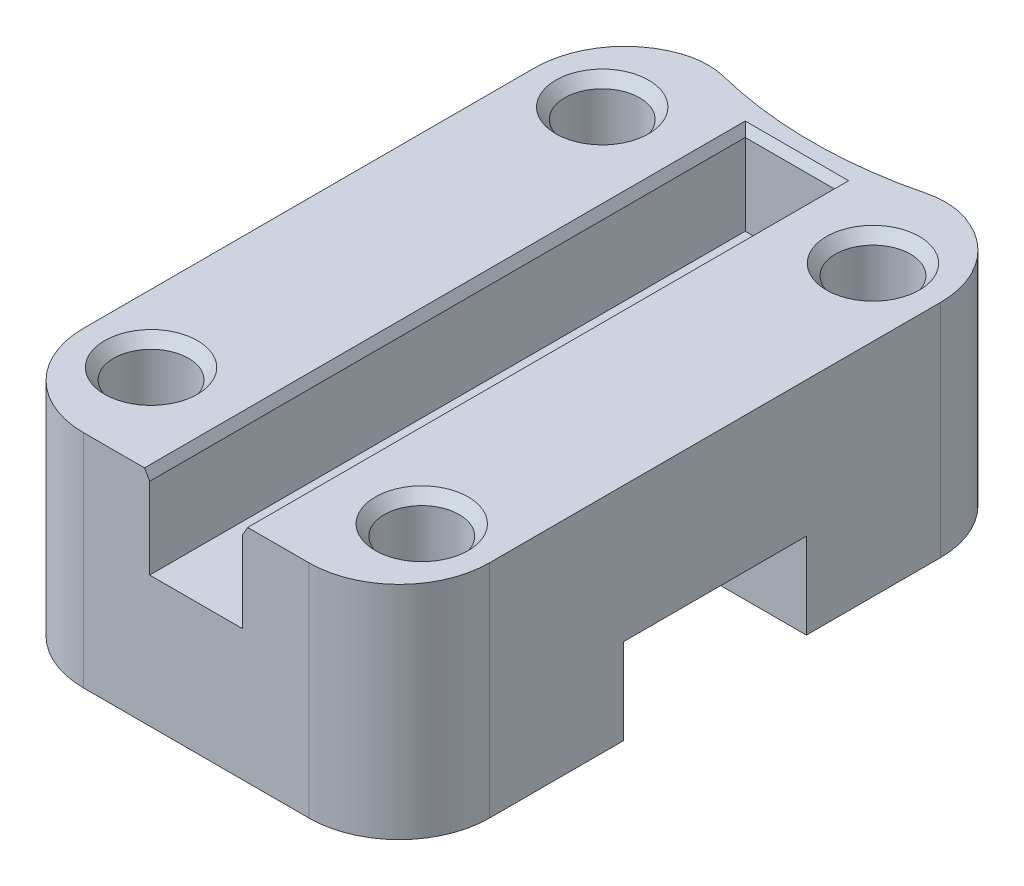
SolidWorks part; units mm, degrees
ref_plane "Спереди" through (0, 0, 0) normal (0, 0, 1) x (1, 0, 0)
ref_plane "Сверху" through (0, 0, 0) normal (0, 1, 0) x (1, 0, 0)
ref_plane "Справа" through (0, 0, 0) normal (1, 0, 0) x (0, 0, -1)
sketch "Sketch1" plane through (0, 0, 0) normal (0, 1, 0) x (1, 0, 0)
  line L1 (22.5, -35) -> (-22.5, -35)
  line L2 (22.5, -35) -> (22.5, 35)
  line L3 (22.5, 35) -> (-22.5, 35)
  line L4 (-22.5, -35) -> (-22.5, 35)
  line L5 (22.5, -35) -> (-22.5, 35) construction
  line L6 (22.5, 35) -> (-22.5, -35) construction
  point P0 (0, 0)
  dimension "D1" = 45
  dimension "D2" = 70
extrude "Boss-Extrude1" add sketch "Sketch1" along normal blind 14.5
sketch "Sketch2" plane through (22.5, 0, 0) normal (1, 0, 0) x (0, 0, -1)
  line L0 (0, 0) -> (0, 14.5) construction
  line L1 (-35, 0) -> (35, 0) construction
  line L2 (-35, 14.5) -> (35, 14.5) construction
  line L4 (10.125, 9.5) -> (-10.125, 9.5)
  line L5 (10.125, 9.5) -> (10.125, 0)
  line L6 (10.125, 0) -> (-10.125, 0)
  line L7 (-10.125, 9.5) -> (-10.125, 0)
  line L8 (10.125, 9.5) -> (-10.125, 0) construction
  line L9 (10.125, 0) -> (-10.125, 9.5) construction
  point P6 (0, 4.75)
  dimension "D1" = 20.25
  dimension "D2" = 9.5
extrude "Cut-Extrude1" cut sketch "Sketch2" against normal through all and the other way through all
sketch "Sketch3" plane through (0, 0, 0) normal (0, -1, 0) x (1, 0, 0)
  line L0 (15, -25) -> (15, 25) construction
  line L1 (-15, 25) -> (-15, -25) construction
  line L2 (-15, -25) -> (15, 25) construction
  line L3 (-22.5, -25) -> (22.5, -25) construction
  line L4 (-22.5, -35) -> (-22.5, -10.125) construction
  line L5 (22.5, -10.125) -> (22.5, -35) construction
  line L6 (-22.5, 25) -> (22.5, 25) construction
  line L7 (-22.5, 10.125) -> (-22.5, 35) construction
  line L8 (22.5, 35) -> (22.5, 10.125) construction
  line L9 (-15, 25) -> (15, -25) construction
  circle A0 centre (15, 25) radius 4.15
  circle A1 centre (15, -25) radius 4.15
  circle A2 centre (-15, -25) radius 4.15
  circle A3 centre (-15, 25) radius 4.15
  point P4 (0, 0)
  dimension "D1" = 8.3
  dimension "D2" = 30
  dimension "D3" = 50
extrude "Cut-Extrude2" cut sketch "Sketch3" against normal through all
sketch "Sketch5" plane through (0, 14.5, 0) normal (0, 1, 0) x (1, 0, 0)
  line L0 (5.15, 35) -> (-5.15, -35) construction
  line L1 (-5.15, -35) -> (-22.5, -35)
  line L2 (-5.15, -35) -> (-5.15, 35) construction
  line L3 (-5.15, 35) -> (-22.5, 35) construction
  line L4 (-22.5, -35) -> (-22.5, 35)
  line L5 (-5.15, -35) -> (-22.5, 35) construction
  line L6 (-5.15, 35) -> (-22.5, -35) construction
  line L7 (5.15, -35) -> (22.5, -35)
  line L8 (5.15, -35) -> (5.15, 35) construction
  line L9 (5.15, 35) -> (22.5, 35) construction
  line L10 (22.5, -35) -> (22.5, 35)
  line L11 (5.15, -35) -> (22.5, 35) construction
  line L12 (5.15, 35) -> (22.5, -35) construction
  line L13 (5.15, -35) -> (-5.15, 35) construction
  line L14 (-5.15, -35) -> (-5.15, 31)
  line L15 (-5.15, 31) -> (5.15, 31)
  line L16 (5.15, 31) -> (5.1302, -34.9493)
  line L17 (5.15, -35) -> (5.1302, -34.9493)
  line L18 (-22.5, 35) -> (22.5, 35)
  circle A0 centre (-15, 25) radius 4.15
  circle A1 centre (15, 25) radius 4.15
  circle A2 centre (15, -25) radius 4.15
  circle A3 centre (-15, -25) radius 4.15
  point P0 (-13.825, 0)
  point P6 (13.825, 0)
  point P12 (0, 0)
  dimension "D1" = 10.3
  dimension "D2" = 4
extrude "Boss-Extrude2" add sketch "Sketch5" along normal blind 10
chamfer "Chamfer1" distance 1 angle 50 4 edges at (15, 24.5, 29.15) (-15, 24.5, 29.15) (-15, 24.5, -20.85) (15, 24.5, -20.85)
chamfer "Chamfer2" distance 1 angle 30 3 edges at (-5.15, 24.5, 2) (0, 24.5, -31) (5.1401, 24.5, 1.9747)
fillet "Fillet1" radius 10 4 edges at (-22.5, 12.25, 35) (22.5, 12.25, 35) (-22.5, 12.25, -35) (22.5, 12.25, -35)
sketch "Sketch6" plane through (0, 0, 0) normal (0, -1, 0) x (1, 0, 0)
  line L1 (12.5, -35) -> (-12.5, -35)
  arc A0 (12.5, -35) -> (-12.5, -35) centre (0, -79.2691) ccw
  dimension "D1" = 46
extrude "Cut-Extrude3" cut sketch "Sketch6" against normal through all
fillet "Fillet2" radius 8 2 edges at (-12.5, 12.25, -35) (12.5, 12.25, -35)
